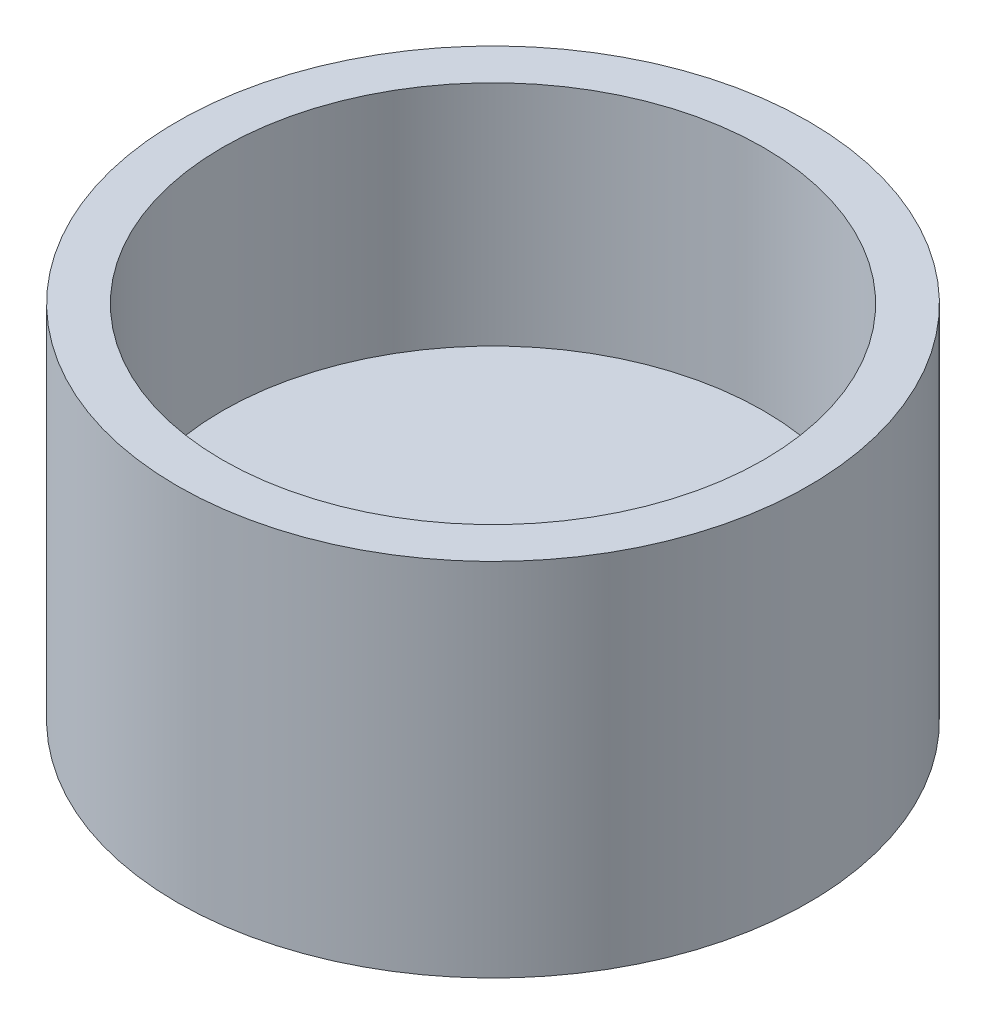
SolidWorks part; units mm, degrees
ref_plane "Front Plane" through (0, 0, 0) normal (0, 0, 1) x (1, 0, 0)
ref_plane "Top Plane" through (0, 0, 0) normal (0, 1, 0) x (1, 0, 0)
ref_plane "Right Plane" through (0, 0, 0) normal (1, 0, 0) x (0, 0, -1)
sketch "Sketch1" plane through (0, 0, 0) normal (0, 1, 0) x (1, 0, 0)
  line L1 (4.7308, 7.2539) -> (-3.9167, 7.724)
  line L2 (-3.9167, 7.724) -> (-8.6475, 0.47)
  line L3 (-8.6475, 0.47) -> (-4.7308, -7.2539)
  line L4 (-4.7308, -7.2539) -> (3.9167, -7.724)
  line L5 (3.9167, -7.724) -> (8.6475, -0.47)
  line L6 (8.6475, -0.47) -> (4.7308, 7.2539)
  circle A0 centre (0, 0) radius 7.5 construction
  circle A1 centre (0, 0) radius 22.225
  dimension "D1" = 15
  dimension "D2" = 44.45
extrude "Boss-Extrude1" add sketch "Sketch1" along normal blind 6.35
sketch "Sketch2" plane through (0, 6.35, 0) normal (0, 1, 0) x (1, 0, 0)
  circle A0 centre (0, 0) radius 22.225
  circle A1 centre (0, 0) radius 19.05
  dimension "D1" = 3.175
extrude "Boss-Extrude2" add sketch "Sketch2" along normal blind 19.05
sketch "Sketch3" plane through (0, 6.35, 0) normal (0, 1, 0) x (1, 0, 0)
  circle A0 centre (0, 0) radius 19.05
  circle A1 centre (0, 0) radius 2.75
  dimension "D1" = 5.5
extrude "Boss-Extrude3" add sketch "Sketch3" along normal blind 3
